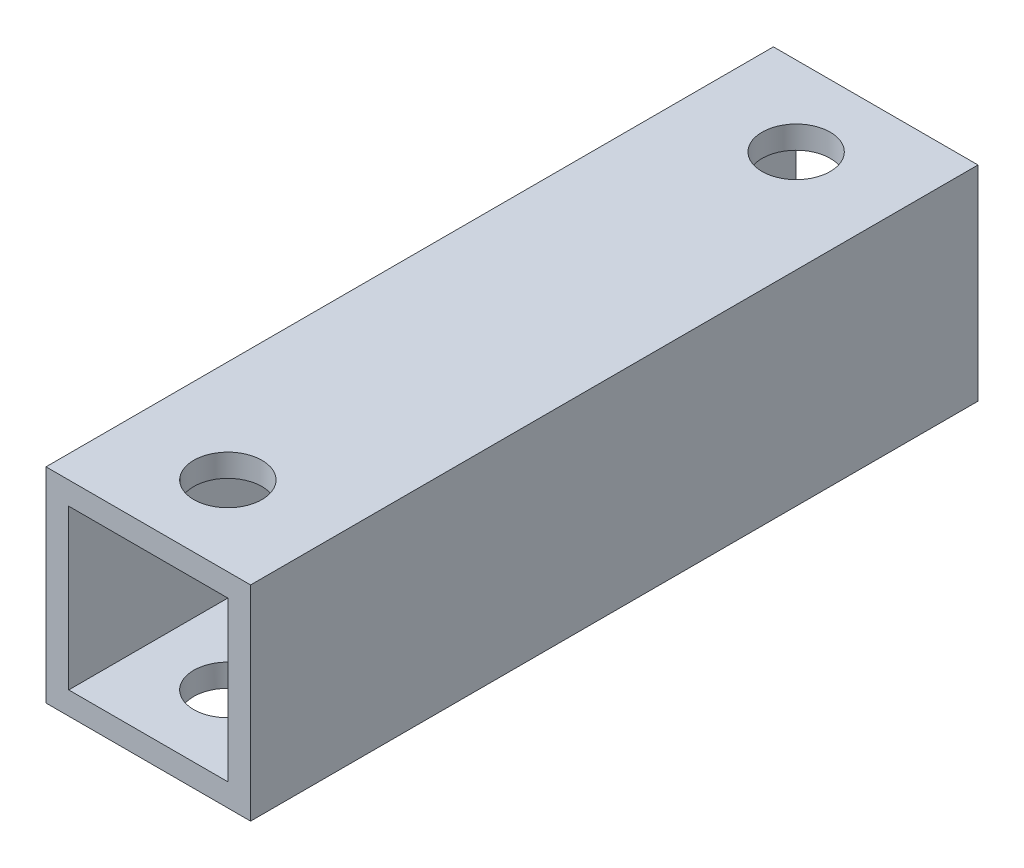
SolidWorks part; units mm, degrees
ref_plane "正面" through (0, 0, 0) normal (0, 0, 1) x (1, 0, 0)
ref_plane "平面" through (0, 0, 0) normal (0, 1, 0) x (1, 0, 0)
ref_plane "右側面" through (0, 0, 0) normal (1, 0, 0) x (0, 0, -1)
sketch "ｽｹｯﾁ1" plane through (0, 0, 0) normal (0, 0, 1) x (1, 0, 0)
  line L1 (-4.5, 4.5) -> (4.5, 4.5)
  line L2 (-4.5, 4.5) -> (-4.5, -4.5)
  line L3 (-4.5, -4.5) -> (4.5, -4.5)
  line L4 (4.5, 4.5) -> (4.5, -4.5)
  line L5 (-4.5, 4.5) -> (4.5, -4.5) construction
  line L6 (-4.5, -4.5) -> (4.5, 4.5) construction
  point P0 (0, 0)
  dimension "D1" = 9
  dimension "D2" = 9
extrude "ﾎﾞｽ - 押し出し1" add sketch "ｽｹｯﾁ1" along normal blind 32
sketch "ｽｹｯﾁ2" plane through (0, 0, 32) normal (0, 0, 1) x (1, 0, 0)
  line L1 (-3.5, 3.5) -> (3.5, 3.5)
  line L2 (-3.5, 3.5) -> (-3.5, -3.5)
  line L3 (-3.5, -3.5) -> (3.5, -3.5)
  line L4 (3.5, 3.5) -> (3.5, -3.5)
  line L5 (-3.5, 3.5) -> (3.5, -3.5) construction
  line L6 (-3.5, -3.5) -> (3.5, 3.5) construction
  point P0 (0, 0)
  dimension "D1" = 7
  dimension "D2" = 7
extrude "ｶｯﾄ - 押し出し1" cut sketch "ｽｹｯﾁ2" against normal blind 40
sketch "ｽｹｯﾁ3" plane through (0, 4.5, 0) normal (0, 1, 0) x (1, 0, 0)
  line L0 (0, 0) -> (0, -3.5)
  line L1 (0, -32) -> (0, -28.5)
  line L2 (4.5, -32) -> (-4.5, -32) construction
  circle A0 centre (0, -3.5) radius 1.5
  circle A1 centre (0, -28.5) radius 1.5
  dimension "D2" = 3
  dimension "D4" = 3
  dimension "D1" = 3.5
  dimension "D3" = 3.5
extrude "ｶｯﾄ - 押し出し2" cut sketch "ｽｹｯﾁ3" against normal blind 38
